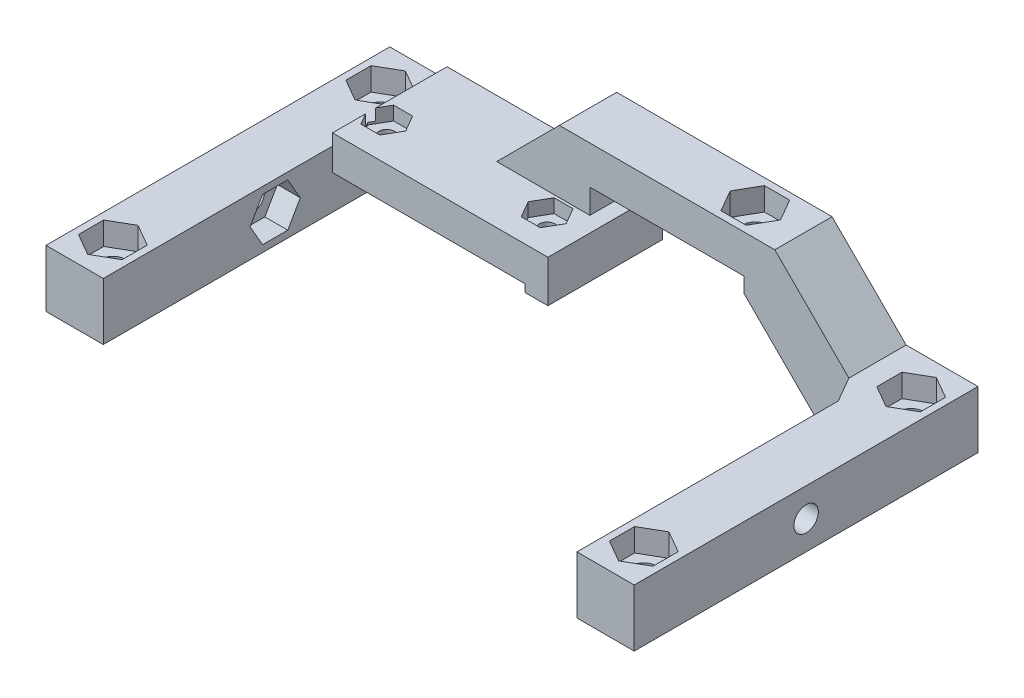
SolidWorks part; units mm, degrees
ref_plane "Alzado" through (0, 0, 0) normal (0, 0, 1) x (1, 0, 0)
ref_plane "Planta" through (0, 0, 0) normal (0, 1, 0) x (1, 0, 0)
ref_plane "Vista lateral" through (0, 0, 0) normal (1, 0, 0) x (0, 0, -1)
sketch "Croquis1" plane through (0, 0, 0) normal (0, 0, 1) x (1, 0, 0)
  line L0 (0, 0) -> (7.5, 0)
  line L1 (7.5, 0) -> (7.5, 4.5)
  line L2 (35.7, 3.5) -> (35.7, 9)
  line L3 (35.7, 9) -> (33.7, 9)
  line L4 (7.5, 4.5) -> (32.7, 4.5)
  line L5 (32.7, 4.5) -> (32.7, 3.5)
  line L6 (32.7, 3.5) -> (35.7, 3.5)
  line L7 (33.7, 9) -> (33.7, 12.2)
  line L8 (33.7, 12.2) -> (53.9, 12.2)
  line L9 (53.9, 12.2) -> (53.9, 10.2)
  line L10 (57.9, 17.2) -> (67.6, 7.5)
  line L11 (53.9, 10.2) -> (64.1, 0)
  line L12 (64.1, 0) -> (77, 0)
  line L13 (77, 0) -> (77, 7.5)
  line L14 (77, 7.5) -> (67.6, 7.5)
  line L15 (29.7, 17.2) -> (21.5, 9)
  line L16 (7.5, 7.5) -> (7.5, 9)
  line L17 (7.5, 9) -> (21.5, 9)
  line L19 (0, 7.5) -> (7.5, 7.5)
  line L20 (0, 7.5) -> (0, 0)
  line L22 (29.7, 17.2) -> (57.9, 17.2)
  dimension "D1" = 7.5
  dimension "D2" = 25.2
  dimension "D3" = 4.5
  dimension "D4" = 1
  dimension "D5" = 3
  dimension "D6" = 7.5
  dimension "D7" = 135
  dimension "D8" = 3.2
  dimension "D9" = 20.2
  dimension "D10" = 2
  dimension "D11" = 5
  dimension "D12" = 2
  dimension "D13" = 4
  dimension "D14" = 7.5
  dimension "D15" = 135
  dimension "D16" = 135
  dimension "D17" = 77
  dimension "D18" = 4
  dimension "D19" = 5.5
extrude "Saliente-Extruir1" add sketch "Croquis1" along normal blind 7.5
sketch "Croquis2" plane through (0, 0, 7.5) normal (0, 0, 1) x (1, 0, 0)
  line L0 (0, 7.5) -> (7.5, 7.5)
  line L1 (35.7, 7.5) -> (35.7, 3.5)
  line L2 (35.7, 3.5) -> (32.7, 3.5)
  line L3 (7.5, 7.5) -> (7.5, 9)
  line L4 (32.7, 3.5) -> (32.7, 4.5)
  line L5 (32.7, 4.5) -> (7.5, 4.5)
  line L6 (7.5, 4.5) -> (7.5, 0)
  line L7 (7.5, 0) -> (0, 0)
  line L8 (0, 0) -> (0, 7.5)
  line L9 (32.7, 4.5) -> (32.7, 3.5) construction
  line L10 (7.5, 9) -> (35.7, 9)
  line L11 (35.7, 9) -> (35.7, 7.5)
extrude "Saliente-Extruir2" add sketch "Croquis2" along normal blind 7.5
ref_plane "Plano1" through (0, 0, 45) normal (0, 0, -1) x (-1, 0, 0)
sketch "Croquis3" plane through (0, 0, 15) normal (0, 0, 1) x (1, 0, 0)
  line L0 (7.5, 7.5) -> (0, 7.5) construction
  line L1 (0, 0) -> (7.5, 0)
  line L2 (0, 0) -> (0, 7.5)
  line L3 (0, 7.5) -> (7.5, 7.5)
  line L4 (7.5, 0) -> (7.5, 7.5)
extrude "Saliente-Extruir3" add sketch "Croquis3" along normal up to surface (30 mm away) up to plane "Plano1"
sketch "Croquis4" plane through (0, 7.5, 0) normal (0, 1, 0) x (1, 0, 0)
  line L0 (67.6, -7.5) -> (69.5, -10.7909)
  line L1 (69.5, -10.7909) -> (69.5, -7.5)
  line L2 (77, -7.5) -> (67.6, -7.5) construction
  line L3 (69.5, -7.5) -> (67.6, -7.5)
  dimension "D1" = 60
  dimension "D2" = 7.5
extrude "Saliente-Extruir4" add sketch "Croquis4" against normal up to surface (7.5 mm away) up to face at (70.55, 0, 3.75)
sketch "Croquis5" plane through (0, 0, 7.5) normal (0, 0, 1) x (1, 0, 0)
  line L4 (69.5, 7.5) -> (69.5, 0)
  line L5 (69.5, 0) -> (77, 0)
  line L6 (77, 0) -> (77, 7.5)
  line L7 (77, 7.5) -> (69.5, 7.5)
  line L8 (69.5, 7.5) -> (69.5, 0)
  line L9 (69.5, 0) -> (77, 0)
  line L10 (77, 0) -> (77, 7.5)
  line L11 (77, 7.5) -> (69.5, 7.5)
  dimension "D1" = 0
extrude "Saliente-Extruir5" add sketch "Croquis5" along normal up to surface (37.5 mm away) up to plane "Plano1"
sketch "Croquis7" plane through (0, 0, 0) normal (0, -1, 0) x (1, 0, 0)
  line L0 (73.25, 45) -> (73.25, 40) construction
  line L1 (77, 45) -> (69.5, 45) construction
  line L2 (73.25, 40) -> (73.25, 5) construction
  line L3 (73.25, 5) -> (73.25, 0) construction
  line L4 (64.1, 0) -> (77, 0) construction
  line L5 (3.75, 0) -> (3.75, 5) construction
  line L6 (0, 0) -> (7.5, 0) construction
  line L7 (3.75, 5) -> (3.75, 40) construction
  line L8 (3.75, 40) -> (3.75, 45) construction
  line L9 (7.5, 45) -> (0, 45) construction
  circle A0 centre (73.25, 5) radius 1.6
  circle A1 centre (73.25, 40) radius 1.6
  circle A2 centre (3.75, 5) radius 1.6
  circle A3 centre (3.75, 40) radius 1.6
  dimension "D2" = 3.2
  dimension "D1" = 35
extrude "Cortar-Extruir1" cut sketch "Croquis7" against normal up to next
sketch "Croquis8" plane through (0, 9, 0) normal (0, 1, 0) x (1, 0, 0)
  line L1 (0.9, -3.3546) -> (0.9, -6.6454)
  line L2 (0.9, -6.6454) -> (3.75, -8.2909)
  line L3 (3.75, -8.2909) -> (6.6, -6.6454)
  line L4 (6.6, -6.6454) -> (6.6, -3.3546)
  line L5 (6.6, -3.3546) -> (3.75, -1.7091)
  line L6 (3.75, -1.7091) -> (0.9, -3.3546)
  line L7 (0.9, -38.3546) -> (0.9, -41.6454)
  line L8 (0.9, -41.6454) -> (3.75, -43.2909)
  line L9 (3.75, -43.2909) -> (6.6, -41.6454)
  line L10 (6.6, -41.6454) -> (6.6, -38.3546)
  line L11 (6.6, -38.3546) -> (3.75, -36.7091)
  line L12 (3.75, -36.7091) -> (0.9, -38.3546)
  line L13 (70.4, -38.3546) -> (70.4, -41.6454)
  line L14 (70.4, -41.6454) -> (73.25, -43.2909)
  line L15 (73.25, -43.2909) -> (76.1, -41.6454)
  line L16 (76.1, -41.6454) -> (76.1, -38.3546)
  line L17 (76.1, -38.3546) -> (73.25, -36.7091)
  line L18 (73.25, -36.7091) -> (70.4, -38.3546)
  line L19 (70.4, -3.3546) -> (70.4, -6.6454)
  line L20 (70.4, -6.6454) -> (73.25, -8.2909)
  line L21 (73.25, -8.2909) -> (76.1, -6.6454)
  line L22 (76.1, -6.6454) -> (76.1, -3.3546)
  line L23 (76.1, -3.3546) -> (73.25, -1.7091)
  line L24 (73.25, -1.7091) -> (70.4, -3.3546)
  circle A0 centre (3.75, -5) radius 2.85 construction
  circle A1 centre (3.75, -40) radius 2.85 construction
  circle A2 centre (73.25, -40) radius 2.85 construction
  circle A3 centre (73.25, -5) radius 2.85 construction
  dimension "D1" = 5.7
extrude "Cortar-Extruir2" cut sketch "Croquis8" against normal blind 4.5
sketch "Croquis9" plane through (0, 12.2, 0) normal (0, -1, 0) x (1, 0, 0)
  line L0 (53.9, 3.75) -> (51.6, 3.75) construction
  line L1 (53.9, 7.5) -> (53.9, 0) construction
  circle A0 centre (51.6, 3.75) radius 1.6
  dimension "D1" = 3.2
  dimension "D2" = 2.3
extrude "Cortar-Extruir3" cut sketch "Croquis9" against normal up to next
sketch "Croquis10" plane through (0, 17.2, 0) normal (0, 1, 0) x (1, 0, 0)
  line L1 (49.9546, -0.9) -> (48.3091, -3.75)
  line L2 (48.3091, -3.75) -> (49.9546, -6.6)
  line L3 (49.9546, -6.6) -> (53.2454, -6.6)
  line L4 (53.2454, -6.6) -> (54.8909, -3.75)
  line L5 (54.8909, -3.75) -> (53.2454, -0.9)
  line L6 (53.2454, -0.9) -> (49.9546, -0.9)
  circle A0 centre (51.6, -3.75) radius 2.85 construction
  dimension "D1" = 5.7
extrude "Cortar-Extruir4" cut sketch "Croquis10" against normal blind 3
sketch "Croquis11" plane through (0, 4.5, 0) normal (0, -1, 0) x (1, 0, 0)
  line L0 (20.1, 0) -> (20.1, 10) construction
  line L1 (7.5, 0) -> (32.7, 0) construction
  line L2 (20.1, 10) -> (9.6, 10) construction
  line L6 (30.6, 10) -> (20.1, 10) construction
  circle A0 centre (30.6, 10) radius 1.05
  circle A1 centre (9.6, 10) radius 1.05
  dimension "D1" = 2.1
  dimension "D2" = 21
  dimension "D3" = 10
extrude "Cortar-Extruir5" cut sketch "Croquis11" against normal up to next
sketch "Croquis12" plane through (0, 9, 0) normal (0, 1, 0) x (1, 0, 0)
  line L1 (8.3587, -12.15) -> (10.8413, -12.15)
  line L2 (10.8413, -12.15) -> (12.0826, -10)
  line L3 (12.0826, -10) -> (10.8413, -7.85)
  line L4 (10.8413, -7.85) -> (8.3587, -7.85)
  line L5 (8.3587, -7.85) -> (7.1174, -10)
  line L6 (7.1174, -10) -> (8.3587, -12.15)
  line L7 (28.1174, -10) -> (29.3587, -12.15)
  line L8 (29.3587, -12.15) -> (31.8413, -12.15)
  line L9 (31.8413, -12.15) -> (33.0826, -10)
  line L10 (33.0826, -10) -> (31.8413, -7.85)
  line L11 (31.8413, -7.85) -> (29.3587, -7.85)
  line L12 (29.3587, -7.85) -> (28.1174, -10)
  circle A0 centre (9.6, -10) radius 2.15 construction
  circle A1 centre (30.6, -10) radius 2.15 construction
  dimension "D1" = 4.3
extrude "Cortar-Extruir6" cut sketch "Croquis12" against normal blind 1.8
sketch "Croquis13" plane through (0, 0, 0) normal (-1, 0, 0) x (0, 0, 1)
  line L0 (45, 3.75) -> (0, 3.75) construction
  line L1 (45, 0) -> (45, 7.5) construction
  line L2 (0, 7.5) -> (0, 0) construction
  circle A0 centre (22.5, 3.75) radius 1.6
  dimension "D1" = 3.2
extrude "Cortar-Extruir7" cut sketch "Croquis13" against normal up to next
sketch "Croquis15" plane through (7.5, 0, 0) normal (1, 0, 0) x (0, 0, -1)
  line L1 (-24.1454, 0.9) -> (-20.8546, 0.9)
  line L2 (-20.8546, 0.9) -> (-19.2091, 3.75)
  line L3 (-19.2091, 3.75) -> (-20.8546, 6.6)
  line L4 (-20.8546, 6.6) -> (-24.1454, 6.6)
  line L5 (-24.1454, 6.6) -> (-25.7909, 3.75)
  line L6 (-25.7909, 3.75) -> (-24.1454, 0.9)
  circle A0 centre (-22.5, 3.75) radius 2.85 construction
  dimension "D1" = 5.7
extrude "Cortar-Extruir8" cut sketch "Croquis15" against normal blind 3
sketch "Croquis16" plane through (77, 0, 0) normal (1, 0, 0) x (0, 0, -1)
  line L0 (-45, 3.75) -> (0, 3.75) construction
  line L1 (-45, 7.5) -> (-45, 0) construction
  line L2 (0, 0) -> (0, 7.5) construction
  circle A0 centre (-22.5, 3.75) radius 1.6
  dimension "D1" = 3.2
extrude "Cortar-Extruir9" cut sketch "Croquis16" against normal up to next
sketch "Croquis17" plane through (69.5, 0, 0) normal (-1, 0, 0) x (0, 0, 1)
  line L1 (20.8546, 0.9) -> (24.1454, 0.9)
  line L2 (24.1454, 0.9) -> (25.7909, 3.75)
  line L3 (25.7909, 3.75) -> (24.1454, 6.6)
  line L4 (24.1454, 6.6) -> (20.8546, 6.6)
  line L5 (20.8546, 6.6) -> (19.2091, 3.75)
  line L6 (19.2091, 3.75) -> (20.8546, 0.9)
  circle A0 centre (22.5, 3.75) radius 2.85 construction
  dimension "D1" = 5.7
extrude "Cortar-Extruir10" cut sketch "Croquis17" against normal blind 3
